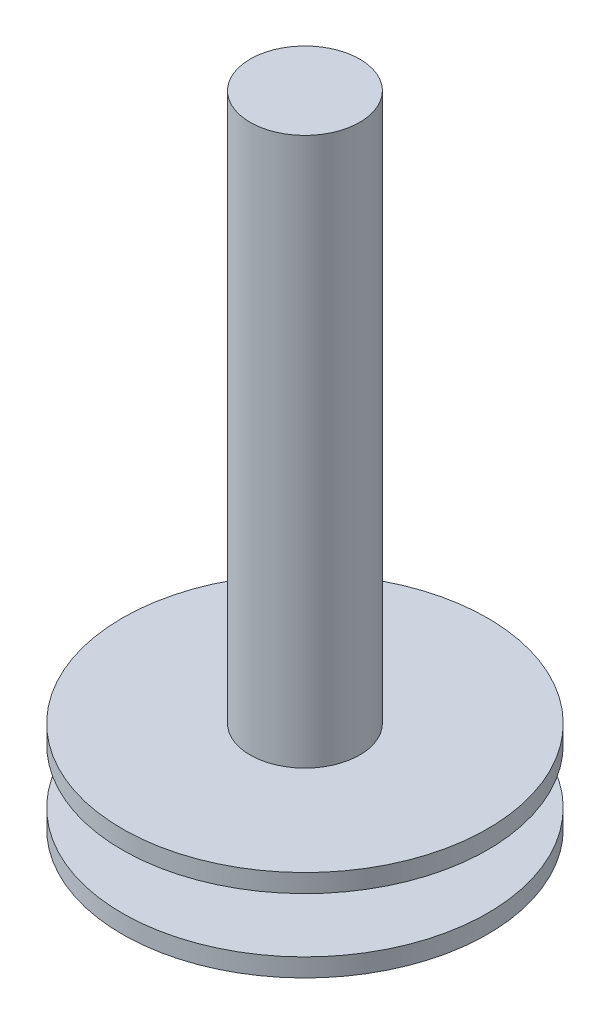
SolidWorks part; units mm, degrees
ref_plane "Front Plane" through (0, 0, 0) normal (0, 0, 1) x (1, 0, 0)
ref_plane "Top Plane" through (0, 0, 0) normal (0, 1, 0) x (1, 0, 0)
ref_plane "Right Plane" through (0, 0, 0) normal (1, 0, 0) x (0, 0, -1)
sketch "Sketch1" plane through (0, 0, 0) normal (0, 0, 1) x (1, 0, 0)
  line L0 (0, 0) -> (10, 0)
  line L1 (10, 0) -> (10, 1)
  line L2 (10, 1) -> (5, 1)
  line L3 (5, 1) -> (5, 4)
  line L4 (5, 4) -> (10, 4)
  line L5 (10, 4) -> (10, 5)
  line L6 (10, 5) -> (0, 5)
  line L7 (0, 5) -> (0, 0)
  dimension "D1" = 10
  dimension "D2" = 5
  dimension "D3" = 1
  dimension "D4" = 1
  dimension "D5" = 5
revolve "Revolve1" add sketch "Sketch1" angle 360 about L7
sketch "Sketch2" plane through (0, 5, 0) normal (0, 1, 0) x (1, 0, 0)
  circle A0 centre (0, 0) radius 3
  dimension "D1" = 6
extrude "Boss-Extrude1" add sketch "Sketch2" along normal blind 30
